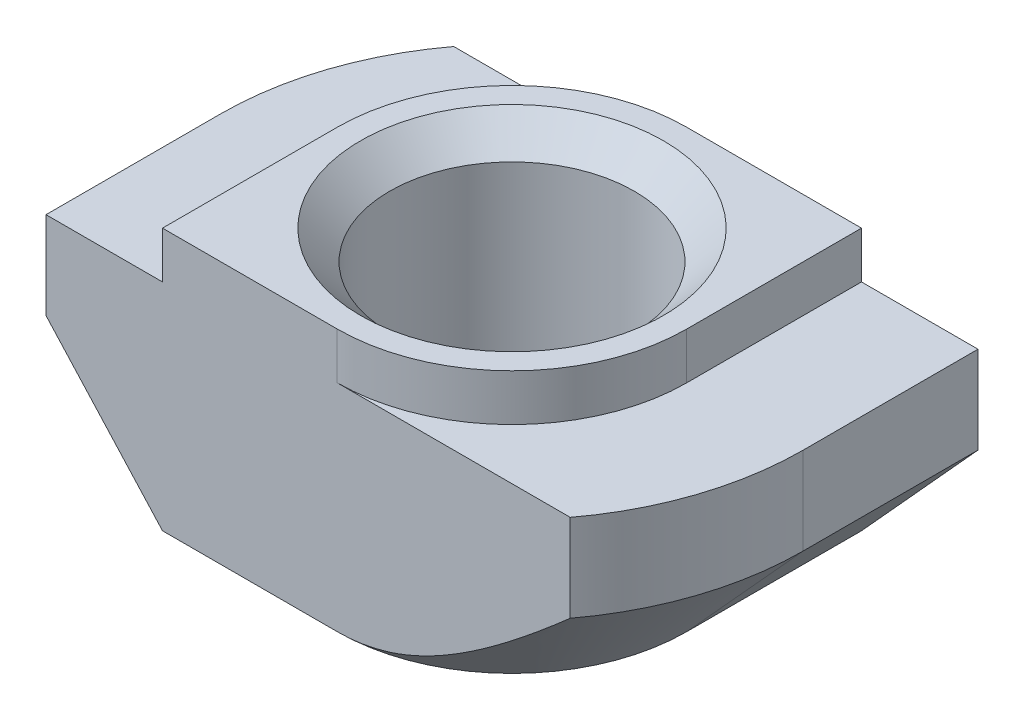
SolidWorks part; units mm, degrees
material "Сталь 20  ГОСТ 1050-2013"
ref_plane "Спереди" through (0, 0, 0) normal (0, 0, 1) x (1, 0, 0)
ref_plane "Сверху" through (0, 0, 0) normal (0, 1, 0) x (1, 0, 0)
ref_plane "Справа" through (0, 0, 0) normal (1, 0, 0) x (0, 0, -1)
sketch "Эскиз1" plane through (0, 0, 0) normal (0, 0, 1) x (1, 0, 0)
  line L0 (3, 0) -> (-3, 0)
  line L1 (-3, 0) -> (-3, -0.8)
  line L2 (-3, -0.8) -> (-5, -0.8)
  line L3 (-5, -0.8) -> (-5, -4.5)
  line L4 (-5, -4.5) -> (5, -4.5)
  line L5 (0, -4.5) -> (0, 0) construction
  line L6 (5, -0.8) -> (5, -4.5)
  line L7 (3, -0.8) -> (5, -0.8)
  line L8 (3, 0) -> (3, -0.8)
  dimension "D1" = 6
  dimension "D2" = 10
  dimension "D3" = 4.5
  dimension "D4" = 0.8
extrude "Бобышка-Вытянуть1" add sketch "Эскиз1" along normal mid plane 6
hole_wizard "Отверстие обработанное метчиком M51" positions "Эскиз2" profile "Эскиз3" tap size "M5" standard "ISO" end condition up to next
sketch "Эскиз2" plane through (0, 0, 0) normal (0, 1, 0) x (1, 0, 0)
  point P0 (0, 0)
sketch "Эскиз3" plane through (0, 0, 0) normal (1, 0, 0) x (0, 0, 1)
  line L0 (0, 0) -> (0, 4.5)
  line L1 (0, 4.5) -> (2.6, 4.5)
  line L2 (2.1, 4) -> (2.1, 0.5)
  line L3 (2.1, 0.5) -> (2.6, 0)
  line L5 (2.6, 0) -> (0, 0)
  line L6 (-2.1, 0.5) -> (-2.6, 0) construction
  line L7 (2.6, 4.5) -> (2.1, 4)
  line L8 (-2.6, 4.5) -> (-2.1, 4) construction
  line L11 (0, -6.35) -> (0, 107.95) construction
  dimension "Диаметр проходного сверла" = 4.2
  dimension "Глубина проходного сверла" = 4.5
  dimension "Диаметр передней зенковки" = 5.2
  dimension "Угол передней зенковки" = 90
  dimension "Диаметр задней зенковки" = 5.2
  dimension "Угол задней зенковки" = 90
cosmetic thread "Отверстие резьбы1" parameters "D2"=5
sketch "Эскиз4" plane through (0, 0, 0) normal (0, 1, 0) x (1, 0, 0)
  line L0 (-3, 3) -> (-3, 0)
  line L1 (-3, -3) -> (-3, 3) construction
  line L2 (3, 3) -> (-3, 3) construction
  line L3 (0, 3) -> (-3, 3)
  line L4 (0, -3) -> (3, -3)
  line L5 (3, -3) -> (-3, -3) construction
  line L6 (3, -3) -> (3, 0)
  line L7 (3, -3) -> (3, 3) construction
  arc A0 (-3, 0) -> (0, 3) centre (0, 0) cw
  arc A1 (3, 0) -> (0, -3) centre (0, 0) cw
extrude "Вырез-Вытянуть1" cut sketch "Эскиз4" against normal up to surface (0.8 mm away) up to face at (-4, -0.8, 0)
sketch "Эскиз5" plane through (0, -0.8, 0) normal (0, 1, 0) x (1, 0, 0)
  line L0 (-5, 0) -> (-5, 3)
  line L1 (-5, -3) -> (-5, 3) construction
  line L2 (-5, 3) -> (-4, 3)
  line L3 (0, 3) -> (-5, 3) construction
  line L4 (5, 0) -> (5, -3)
  line L5 (5, -3) -> (5, 3) construction
  line L6 (5, -3) -> (4, -3)
  line L7 (5, -3) -> (0, -3) construction
  arc A0 (-4, 3) -> (-5, 0) centre (0, 0) ccw
  arc A2 (5, 0) -> (4, -3) centre (0, 0) cw
  point P19 (0, 0)
extrude "Вырез-Вытянуть2" cut sketch "Эскиз5" against normal through all
sketch "Эскиз6" plane through (0, 0, 3) normal (0, 0, 1) x (1, 0, 0)
  line L0 (-5, -2.3) -> (-5, -4.5)
  line L1 (-5, -0.8) -> (-5, -4.5) construction
  line L2 (-5, -4.5) -> (-3, -4.5)
  line L3 (-5, -4.5) -> (4, -4.5) construction
  line L4 (-3, -4.5) -> (-5, -2.3)
  line L5 (-3, -0.8) -> (-5, -0.8) construction
  line L6 (-3, 0) -> (-3, -0.8) construction
  point P10 (0, 0)
  dimension "D1" = 1.5
sketch "Эскиз7" plane through (0, -4.5, 0) normal (0, -1, 0) x (1, 0, 0)
  line L0 (0, 5) -> (-5, 5)
  line L1 (-5, 5) -> (-5, 0)
  line L2 (0, -5) -> (5, -5)
  line L3 (5, -5) -> (5, 0)
  arc A0 (-5, 0) -> (0, -5) centre (0, 0) ccw
  arc A1 (5, 0) -> (0, 5) centre (0, 0) ccw
sweep "Вырез-По траектории1" cut profiles "Эскиз6" path "Эскиз7"
